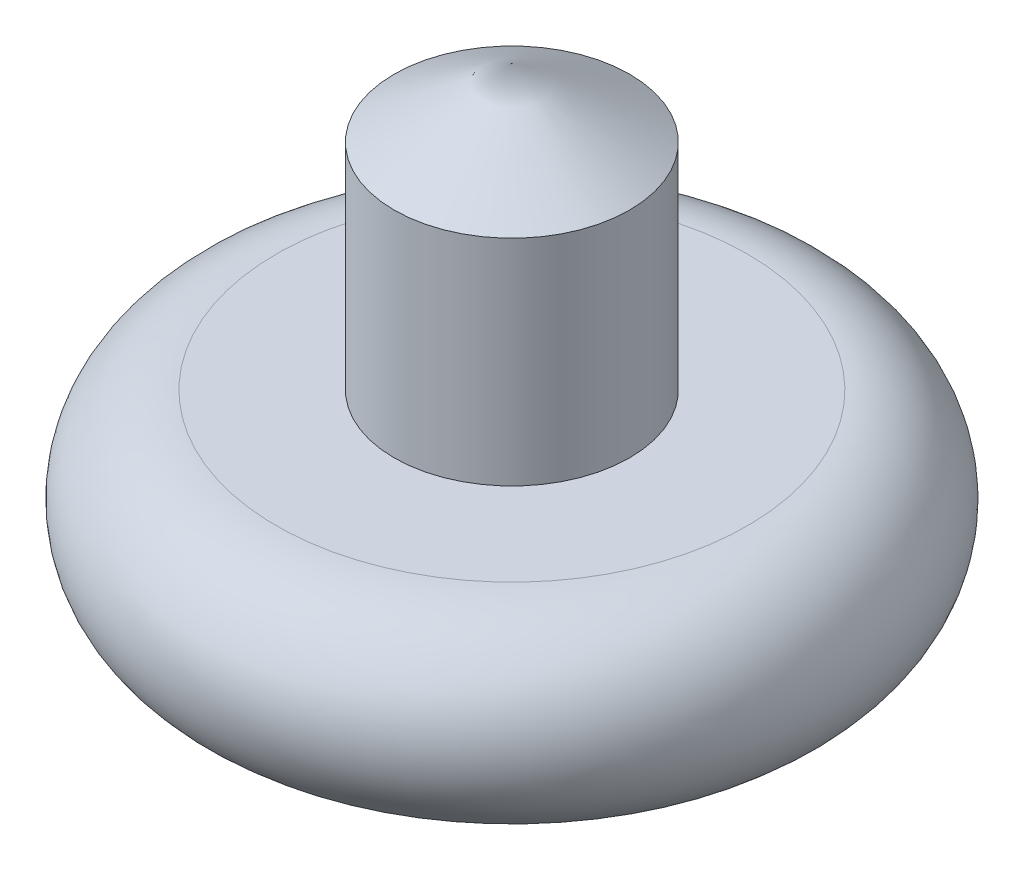
SolidWorks part; units mm, degrees
ref_plane "Front Plane" through (0, 0, 0) normal (0, 0, 1) x (1, 0, 0)
ref_plane "Top Plane" through (0, 0, 0) normal (0, 1, 0) x (1, 0, 0)
ref_plane "Right Plane" through (0, 0, 0) normal (1, 0, 0) x (0, 0, -1)
sketch "Sketch4" plane through (0, 0, 0) normal (0, 0, 1) x (1, 0, 0)
  line L0 (0, 0) -> (0, 200)
  line L1 (0, 0) -> (100, 0)
  line L3 (100, 80) -> (50, 80)
  line L4 (50, 80) -> (50, 171.1325)
  line L5 (50, 171.1325) -> (0, 200)
  arc A0 (100, 0) -> (100, 80) centre (100, 40) ccw
  dimension "D5" = 40
  dimension "D1" = 200
  dimension "D2" = 100
  dimension "D3" = 50
  dimension "D4" = 60
revolve "Revolve1" add sketch "Sketch4" angle 360 about L0
